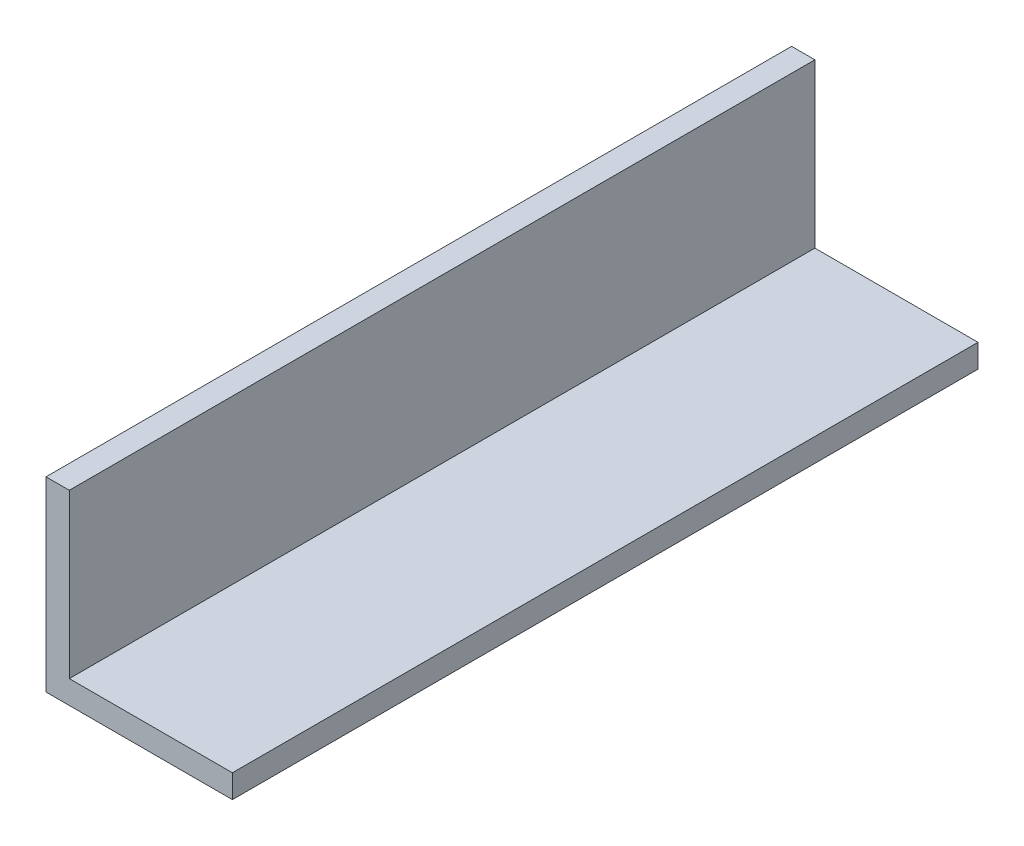
SolidWorks part; units mm, degrees
ref_plane "Front Plane" through (0, 0, 0) normal (0, 0, 1) x (1, 0, 0)
ref_plane "Top Plane" through (0, 0, 0) normal (0, 1, 0) x (1, 0, 0)
ref_plane "Right Plane" through (0, 0, 0) normal (1, 0, 0) x (0, 0, -1)
sketch "Sketch1" plane through (0, 0, 0) normal (0, 0, 1) x (1, 0, 0)
  line L0 (0, 25.4) -> (0, 0)
  line L1 (0, 0) -> (25.4, 0)
  line L2 (25.4, 0) -> (25.4, 3.175)
  line L3 (25.4, 3.175) -> (3.175, 3.175)
  line L4 (3.175, 3.175) -> (3.175, 25.4)
  line L5 (3.175, 25.4) -> (0, 25.4)
  dimension "D1" = 3.175
  dimension "D2" = 25.4
extrude "Boss-Extrude1" add sketch "Sketch1" along normal mid plane 101.6
